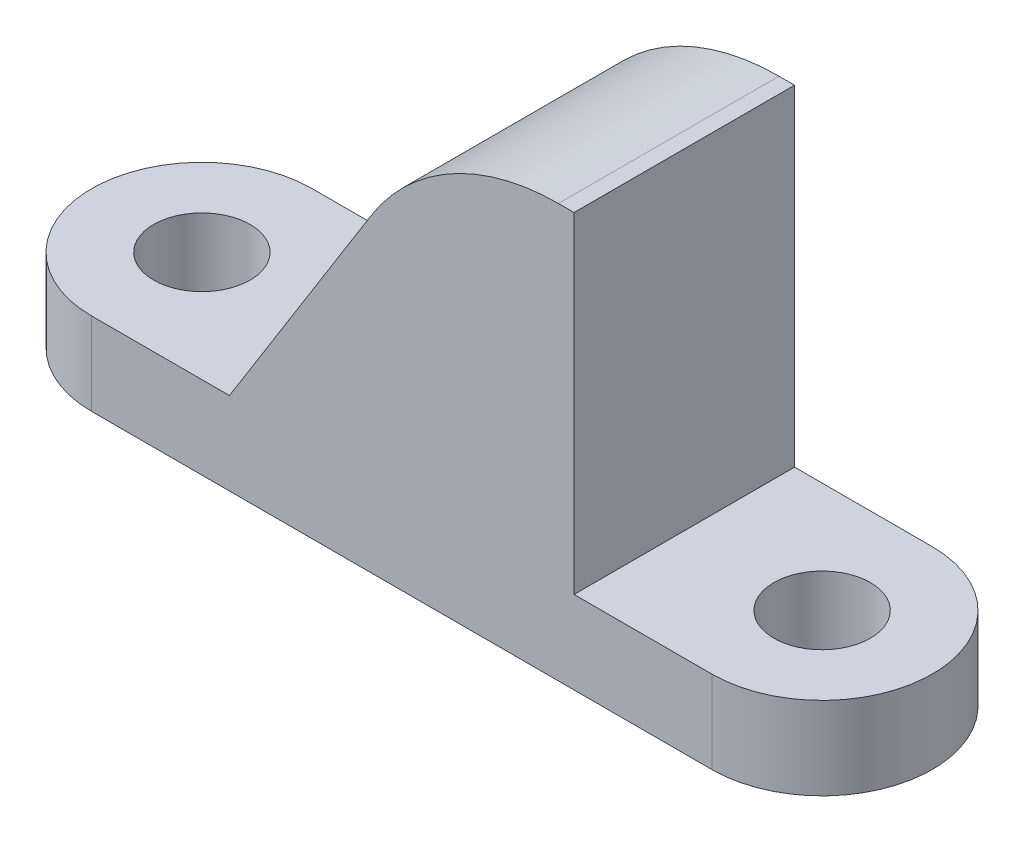
SolidWorks part; units mm, degrees
ref_plane "Front Plane" through (0, 0, 0) normal (0, 0, 1) x (1, 0, 0)
ref_plane "Top Plane" through (0, 0, 0) normal (0, 1, 0) x (1, 0, 0)
ref_plane "Right Plane" through (0, 0, 0) normal (1, 0, 0) x (0, 0, -1)
sketch "Sketch1" plane through (0, 0, 0) normal (0, 1, 0) x (1, 0, 0)
  line L0 (0, 0) -> (-11.25, 0) construction
  line L1 (-11.25, -4) -> (11.25, -4)
  line L2 (-11.25, -4) -> (-11.25, 4) construction
  line L3 (-11.25, 4) -> (11.25, 4)
  line L4 (11.25, -4) -> (11.25, 4) construction
  line L5 (-11.25, -4) -> (11.25, 4) construction
  line L6 (-11.25, 4) -> (11.25, -4) construction
  line L7 (0, 0) -> (0, 7.0959) construction
  circle A0 centre (-11.25, 0) radius 1.75
  arc A1 (-11.25, 4) -> (-11.25, -4) centre (-11.25, 0) ccw
  arc A2 (11.25, 4) -> (11.25, -4) centre (11.25, 0) cw
  circle A3 centre (11.25, 0) radius 1.75
  point P0 (0, 0)
  dimension "D1" = 3.5
  dimension "D2" = 11.25
  dimension "D3" = 4
extrude "Boss-Extrude1" add sketch "Sketch1" along normal blind 3
sketch "Sketch2" plane through (0, 3, 0) normal (0, 1, 0) x (1, 0, 0)
  line L0 (11.25, 4) -> (-11.25, 4) construction
  line L1 (1.25, -4) -> (6.25, -4)
  line L2 (1.25, -4) -> (1.25, 4)
  line L3 (1.25, 4) -> (6.25, 4)
  line L4 (6.25, -4) -> (6.25, 4)
  line L5 (1.25, -4) -> (6.25, 4) construction
  line L6 (1.25, 4) -> (6.25, -4) construction
  circle A0 centre (11.25, 0) radius 1.75 construction
  point P0 (3.75, 0)
  dimension "D1" = 5
  dimension "D2" = 5
extrude "Boss-Extrude2" add sketch "Sketch2" along normal blind 12
sketch "Sketch3" plane through (0, 0, 4) normal (0, 0, 1) x (1, 0, 0)
  line L0 (1.25, 15) -> (-6.25, 3)
  line L1 (-11.25, 3) -> (1.25, 3) construction
  line L2 (-6.25, 3) -> (1.25, 3)
  line L3 (1.25, 3) -> (1.25, 15)
  line L5 (-11.25, 3) -> (-11.25, 0) construction
  dimension "D1" = 5
extrude "Boss-Extrude3" add sketch "Sketch3" against normal blind 8
fillet "Fillet2" radius 8 1 edges at (1.25, 15, 0)
